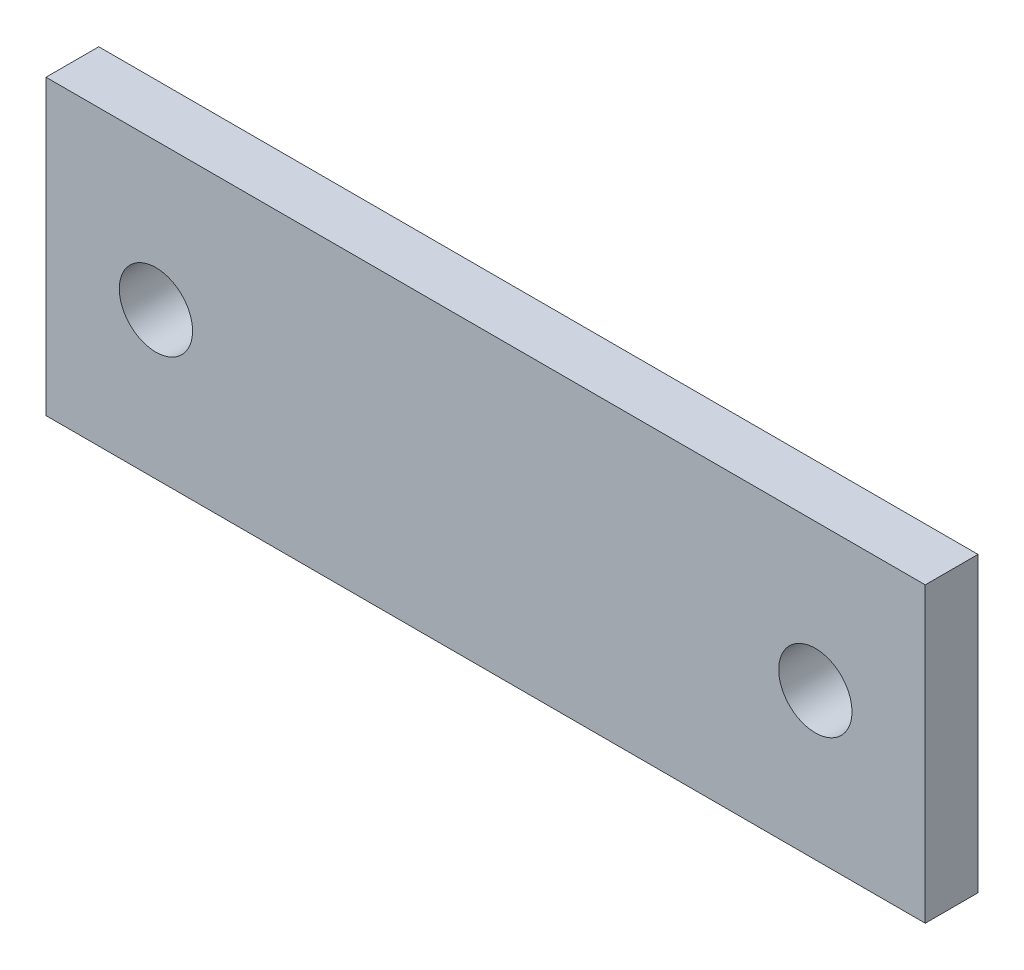
SolidWorks part; units mm, degrees
ref_plane "Front" through (0, 0, 0) normal (0, 0, 1) x (1, 0, 0)
ref_plane "Top" through (0, 0, 0) normal (0, 1, 0) x (1, 0, 0)
ref_plane "Right" through (0, 0, 0) normal (1, 0, 0) x (0, 0, -1)
sketch "Sketch1" plane through (0, 0, 0) normal (0, 0, 1) x (1, 0, 0)
  line L0 (-38.1, 12.7) -> (38.1, -12.7) construction
  line L1 (-38.1, 12.7) -> (38.1, 12.7)
  line L2 (-38.1, 12.7) -> (-38.1, -12.7)
  line L3 (-38.1, -12.7) -> (38.1, -12.7)
  line L4 (38.1, 12.7) -> (38.1, -12.7)
  line L6 (-28.575, 0) -> (28.575, 0) construction
  circle A0 centre (-28.575, 0) radius 3.175
  circle A1 centre (28.575, 0) radius 3.175
  dimension "Hole Size" = 6.35
  dimension "A1" = 76.2
  dimension "B" = 25.4
  dimension "Hole Spacing" = 57.15
extrude "Boss-Extrude1" add sketch "Sketch1" against normal blind 4.572
